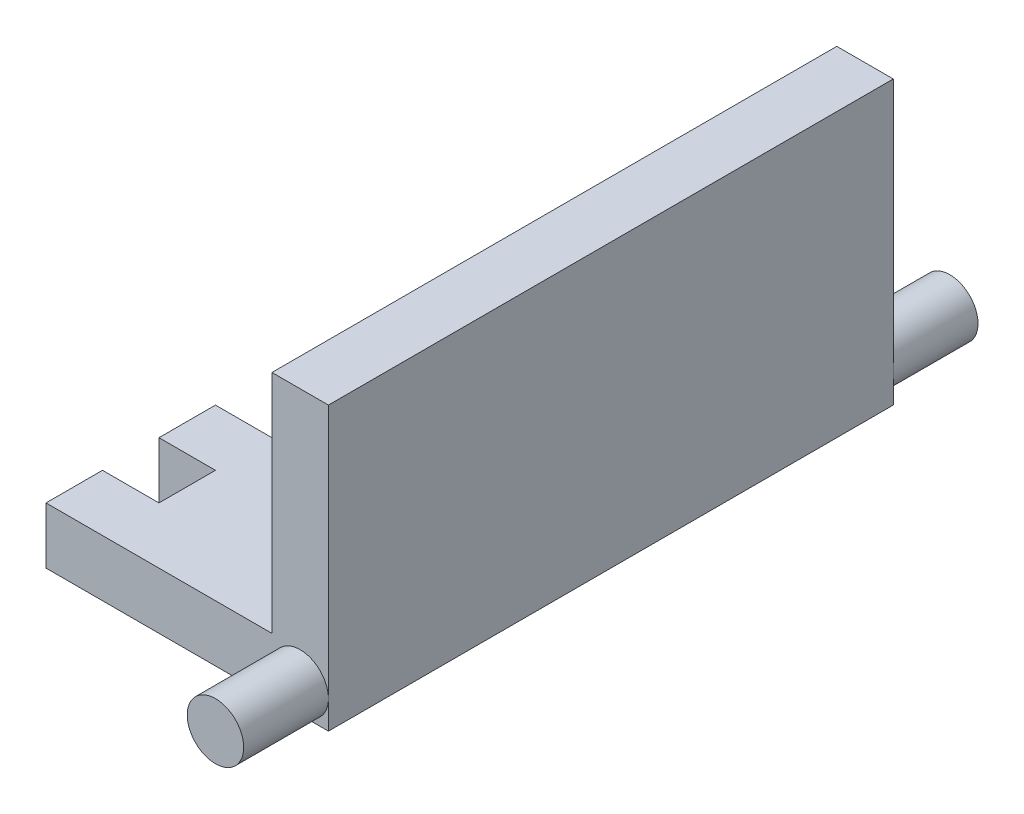
SolidWorks part; units mm, degrees
ref_plane "Plan de face" through (0, 0, 0) normal (0, 0, 1) x (1, 0, 0)
ref_plane "Plan de dessus" through (0, 0, 0) normal (0, 1, 0) x (1, 0, 0)
ref_plane "Plan de droite" through (0, 0, 0) normal (1, 0, 0) x (0, 0, -1)
sketch "Esquisse1" plane through (0, 0, 0) normal (0, 0, 1) x (1, 0, 0)
  line L1 (0, 0) -> (-50, 0)
  line L2 (0, 0) -> (0, 10)
  line L3 (0, 10) -> (-50, 10)
  line L4 (-50, 0) -> (-50, 10)
  dimension "D1" = 10
  dimension "D2" = 50
extrude "Boss.-Extru.1" add sketch "Esquisse1" along normal blind 100
sketch "Esquisse2" plane through (0, 0, 100) normal (0, 0, 1) x (1, 0, 0)
  line L0 (0, 10) -> (-50, 10) construction
  line L1 (-50, 0) -> (0, 0) construction
  line L2 (0, 0) -> (0, 10) construction
  circle A0 centre (-5, 5) radius 5
extrude "Boss.-Extru.2" add sketch "Esquisse2" along normal blind 15
sketch "Esquisse3" plane through (0, 0, 0) normal (0, 0, -1) x (-1, 0, 0)
  line L0 (0, 10) -> (50, 10) construction
  line L1 (50, 0) -> (0, 0) construction
  line L2 (0, 0) -> (0, 10) construction
  circle A0 centre (5, 5) radius 5
extrude "Boss.-Extru.3" add sketch "Esquisse3" along normal blind 15
sketch "Esquisse4" plane through (0, 10, 0) normal (0, 1, 0) x (1, 0, 0)
  line L1 (-50, 0) -> (-40, 0)
  line L2 (-50, 0) -> (-50, -10)
  line L3 (-50, -10) -> (-40, -10)
  line L4 (-40, 0) -> (-40, -10)
  dimension "D1" = 10
  dimension "D2" = 10
extrude "Enlèv. mat.-Extru.1" cut sketch "Esquisse4" against normal blind 15
pattern_linear "Répétition linéaire1" count 5 spacing 20 along (0, 0, 1) of "Enlèv. mat.-Extru.1"
sketch "Esquisse5" plane through (0, 10, 0) normal (0, 1, 0) x (1, 0, 0)
  line L0 (-5, 0) -> (-40, 0) construction
  line L1 (0, -100) -> (-10, -100)
  line L2 (0, -100) -> (0, 0)
  line L3 (0, 0) -> (-10, 0)
  line L4 (-10, -100) -> (-10, 0)
  dimension "D1" = 10
extrude "Boss.-Extru.4" add sketch "Esquisse5" along normal blind 40
